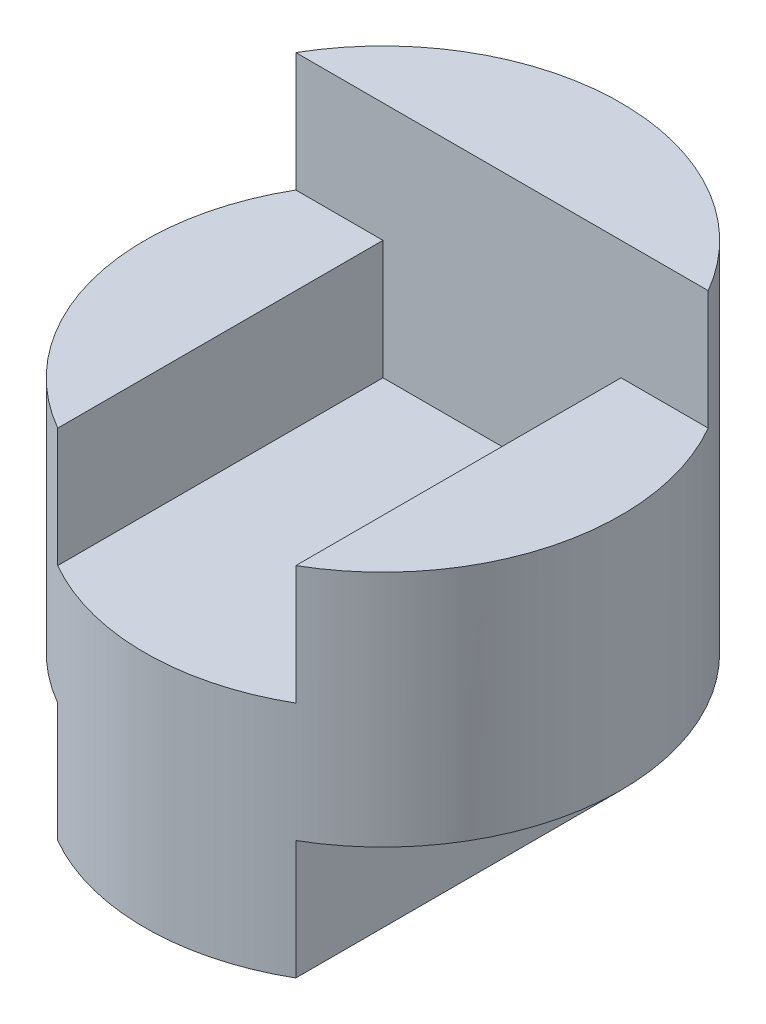
SolidWorks part; units mm, degrees
ref_plane "Front" through (0, 0, 0) normal (0, 0, 1) x (1, 0, 0)
ref_plane "Top" through (0, 0, 0) normal (0, 1, 0) x (1, 0, 0)
ref_plane "Right" through (0, 0, 0) normal (1, 0, 0) x (0, 0, -1)
sketch "Sketch1" plane through (0, 0, 0) normal (0, 1, 0) x (1, 0, 0)
  circle A0 centre (0, 0) radius 2
  dimension "D1" = 4
extrude "Boss-Extrude1" add sketch "Sketch1" along normal blind 4
sketch "Sketch2" plane through (0, 0, 0) normal (0, 0, 1) x (1, 0, 0)
  line L1 (-2, 0) -> (-1, 0)
  line L2 (-2, 0) -> (-2, 1)
  line L3 (-2, 1) -> (-1, 1)
  line L4 (-1, 0) -> (-1, 1)
  line L13 (2, 0) -> (1, 0)
  line L14 (2, 0) -> (2, 1)
  line L15 (2, 1) -> (1, 1)
  line L16 (1, 0) -> (1, 1)
  dimension "D1" = 1
  dimension "D2" = 1
  dimension "D3" = 1
  dimension "D4" = 1
extrude "Cut-Extrude1" cut sketch "Sketch2" against normal mid plane 4
sketch "Sketch3" plane through (0, 0, 0) normal (0, 0, 1) x (1, 0, 0)
  line L0 (-2, 4) -> (2, 4)
  line L1 (2, 4) -> (2, 3)
  line L2 (2, 1) -> (2, 4) construction
  line L3 (2, 3) -> (1, 3)
  line L4 (1, 3) -> (1, 2)
  line L5 (1, 2) -> (-1, 2)
  line L6 (-1, 2) -> (-1, 3)
  line L7 (-1, 3) -> (-2, 3)
  line L8 (-2, 4) -> (-2, 1) construction
  line L9 (-2, 3) -> (-2, 4)
  dimension "D1" = 1
  dimension "D2" = 1
  dimension "D3" = 1
  dimension "D4" = 1
extrude "Cut-Extrude2" cut sketch "Sketch3" against normal blind 1 and the other way blind 4
sketch "Sketch4" plane through (0, 0, 0) normal (1, 0, 0) x (0, 0, -1)
  line L0 (1.7321, 1) -> (-1.7321, 1) construction
  line L1 (2, 0) -> (1, 0)
  line L2 (2, 0) -> (2, 1)
  line L3 (2, 1) -> (1, 1)
  line L4 (1, 0) -> (1, 1)
  dimension "D1" = 1
extrude "Cut-Extrude3" cut sketch "Sketch4" against normal mid plane 10
